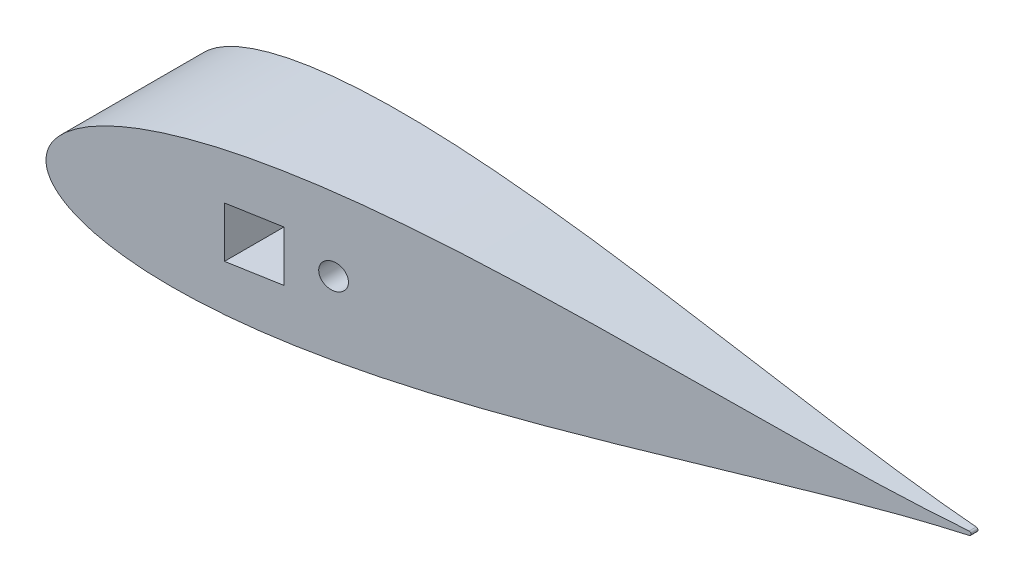
SolidWorks part; units mm, degrees
ref_plane "Front Plane" through (0, 0, 0) normal (0, 0, 1) x (1, 0, 0)
ref_plane "Top Plane" through (0, 0, 0) normal (0, 1, 0) x (1, 0, 0)
ref_plane "Right Plane" through (0, 0, 0) normal (1, 0, 0) x (0, 0, -1)
curve "Curve4"
  spline degree 3 poles (100, 0, 0) (99.8498, 0.0023, 0) (99.4759, 0.008, 0) (99.1023, 0.0238, 0) (98.8789, 0.0332, 0) knots 0 0 0 0 0.401829 1 1 1 1
curve "Curve5"
  spline degree 3 poles (99.3714, -0.0082, 0) (100.2526, 0, 0) (99.3714, 0.0082, 0) (98.8504, 0.035, 0) (97.904, 0.0811, 0) (96.8285, 0.1543, 0) (95.5159, 0.2583, 0) (94.013, 0.3972, 0) (92.313, 0.574, 0) (90.4281, 0.791, 0) (88.3655, 1.0495, 0) (86.1348, 1.3497, 0) (83.7456, 1.691, 0) (81.2082, 2.0715, 0) (78.5335, 2.4886, 0) (75.7326, 2.9386, 0) (72.8172, 3.4168, 0) (69.799, 3.9177, 0) (66.6904, 4.435, 0) (63.5039, 4.9616, 0) (60.2521, 5.4899, 0) (56.948, 6.0119, 0) (53.6049, 6.519, 0) (50.2363, 7.0024, 0) (46.8558, 7.4534, 0) (43.4774, 7.8632, 0) (40.1152, 8.2232, 0) (36.7837, 8.5249, 0) (33.4975, 8.7606, 0) (30.2716, 8.923, 0) (27.1211, 9.0055, 0) (24.0614, 9.0025, 0) (21.108, 8.909, 0) (18.277, 8.7213, 0) (15.5843, 8.4369, 0) (13.0466, 8.0543, 0) (10.6806, 7.5735, 0) (8.5039, 6.996, 0) (6.5349, 6.3253, 0) (4.7933, 5.5673, 0) (3.3001, 4.7321, 0) (2.0777, 3.8366, 0) (1.1467, 2.91, 0) (0.5165, 2.0014, 0) (0.165, 1.1816, 0) (0.0231, 0.524, 0) (-0.0093, 0, 0) (0.0231, -0.524, 0) (0.165, -1.1816, 0) (0.5165, -2.0014, 0) (1.1467, -2.91, 0) (2.0777, -3.8366, 0) (3.3001, -4.7321, 0) (4.7933, -5.5673, 0) (6.5349, -6.3253, 0) (8.5039, -6.996, 0) (10.6806, -7.5735, 0) (13.0466, -8.0543, 0) (15.5843, -8.4369, 0) (18.277, -8.7213, 0) (21.108, -8.909, 0) (24.0614, -9.0025, 0) (27.1211, -9.0055, 0) (30.2716, -8.923, 0) (33.4975, -8.7606, 0) (36.7837, -8.5249, 0) (40.1152, -8.2232, 0) (43.4774, -7.8632, 0) (46.8558, -7.4534, 0) (50.2363, -7.0024, 0) (53.6049, -6.519, 0) (56.948, -6.0119, 0) (60.2521, -5.4899, 0) (63.5039, -4.9616, 0) (66.6904, -4.435, 0) (69.799, -3.9177, 0) (72.8172, -3.4168, 0) (75.7326, -2.9386, 0) (78.5335, -2.4886, 0) (81.2082, -2.0715, 0) (83.7456, -1.691, 0) (86.1348, -1.3497, 0) (88.3655, -1.0495, 0) (90.4281, -0.791, 0) (92.313, -0.574, 0) (94.013, -0.3972, 0) (95.5159, -0.2583, 0) (96.8285, -0.1543, 0) (97.904, -0.0811, 0) (98.8504, -0.035, 0) (99.3714, -0.0082, 0) (100.2526, 0, 0) (99.3714, 0.0082, 0) knots -0.009667 -0.005395 -0.002168 0 0.002168 0.005395 0.009667 0.014967 0.021271 0.028553 0.036781 0.04592 0.055932 0.066773 0.078397 0.090755 0.103793 0.117456 0.131686 0.146422 0.1616 0.177156 0.193024 0.209135 0.225421 0.241812 0.258238 0.274629 0.290914 0.307025 0.322893 0.338448 0.353626 0.368361 0.38259 0.396253 0.40929 0.421647 0.43327 0.444109 0.454119 0.463255 0.471479 0.478755 0.485052 0.490344 0.49461 0.497833 0.5 0.502167 0.50539 0.509656 0.514948 0.521245 0.528521 0.536745 0.545881 0.555891 0.56673 0.578353 0.59071 0.603747 0.61741 0.631639 0.646374 0.661552 0.677107 0.692975 0.709086 0.725371 0.741762 0.758188 0.774579 0.790865 0.806976 0.822844 0.8384 0.853578 0.868314 0.882544 0.896207 0.909245 0.921603 0.933227 0.944068 0.95408 0.963219 0.971447 0.978729 0.985033 0.990333 0.994605 0.997832 1 1.002168 1.005395 1.009667 periodic
sketch "Sketch2" plane through (0, 0, 0) normal (0, 0, 1) x (1, 0, 0)
  line L0 (642.3793, 0) -> (0, 0) construction
  circle A14 centre (642.3793, 0) radius 1.5875 construction
  arc A15 (642.5108, -1.582) -> (642.5108, 1.582) centre (642.3793, 0) ccw
  spline S2 degree 3 poles (666.3448, -0.0547) (672.2538, 0) (666.3448, 0.0547) (662.8509, 0.2344) (656.505, 0.5436) (649.293, 1.0348) (640.4916, 1.7319) (630.4138, 2.6634) (619.0141, 3.8493) (606.375, 5.3044) (592.5439, 7.0376) (577.5855, 9.0506) (561.5643, 11.3389) (544.5497, 13.8907) (526.6141, 16.6877) (507.8326, 19.7051) (488.2827, 22.9117) (468.0444, 26.2704) (447.1994, 29.739) (425.8316, 33.2703) (404.0263, 36.8132) (381.8707, 40.3133) (359.4533, 43.7135) (336.8645, 46.9554) (314.1962, 49.9798) (291.5418, 52.7277) (268.9963, 55.1412) (246.6566, 57.1646) (224.6209, 58.7452) (202.9892, 59.8341) (181.8631, 60.3875) (161.3458, 60.367) (141.542, 59.7399) (122.5581, 58.4818) (104.5023, 56.5743) (87.485, 54.0089) (71.6197, 50.7848) (57.0237, 46.9125) (43.8205, 42.415) (32.1416, 37.3322) (22.1291, 31.7315) (13.9324, 25.7264) (7.6896, 19.5132) (3.4631, 13.4204) (1.1063, 7.9234) (0.1546, 3.5138) (-0.0622, 0) (0.1546, -3.5138) (1.1063, -7.9234) (3.4631, -13.4204) (7.6896, -19.5132) (13.9324, -25.7264) (22.1291, -31.7315) (32.1416, -37.3322) (43.8205, -42.415) (57.0237, -46.9125) (71.6197, -50.7848) (87.485, -54.0089) (104.5023, -56.5743) (122.5581, -58.4818) (141.542, -59.7399) (161.3458, -60.367) (181.8631, -60.3875) (202.9892, -59.8341) (224.6209, -58.7452) (246.6566, -57.1646) (268.9963, -55.1412) (291.5418, -52.7277) (314.1962, -49.9798) (336.8645, -46.9554) (359.4533, -43.7135) (381.8707, -40.3133) (404.0263, -36.8132) (425.8316, -33.2703) (447.1994, -29.739) (468.0444, -26.2704) (488.2827, -22.9117) (507.8326, -19.7051) (526.6141, -16.6877) (544.5497, -13.8907) (561.5643, -11.3389) (577.5855, -9.0506) (592.5439, -7.0376) (606.375, -5.3044) (619.0141, -3.8493) (630.4138, -2.6634) (640.4916, -1.7319) (649.293, -1.0348) (656.505, -0.5436) (662.8509, -0.2344) (666.3448, -0.0547) (672.2538, 0) (666.3448, 0.0547) knots -0.009667 -0.005395 -0.002168 0 0.002168 0.005395 0.009667 0.014967 0.021271 0.028553 0.036781 0.04592 0.055932 0.066773 0.078397 0.090755 0.103793 0.117456 0.131686 0.146422 0.1616 0.177156 0.193024 0.209135 0.225421 0.241812 0.258238 0.274629 0.290914 0.307025 0.322893 0.338448 0.353626 0.368361 0.38259 0.396253 0.40929 0.421647 0.43327 0.444109 0.454119 0.463255 0.471479 0.478755 0.485052 0.490344 0.49461 0.497833 0.5 0.502167 0.50539 0.509656 0.514948 0.521245 0.528521 0.536745 0.545881 0.555891 0.56673 0.578353 0.59071 0.603747 0.61741 0.631639 0.646374 0.661552 0.677107 0.692975 0.709086 0.725371 0.741762 0.758188 0.774579 0.790865 0.806976 0.822844 0.8384 0.853578 0.868314 0.882544 0.896207 0.909245 0.921603 0.933227 0.944068 0.95408 0.963219 0.971447 0.978729 0.985033 0.990333 0.994605 0.997832 1 1.002168 1.005395 1.009667 only from (670.56, 0) to (670.56, 0)
  point P8 (1.2169, -4.6585)
  point P10 (1.2169, 4.6585)
  dimension "D10" = 3.175
extrude "Boss-Extrude1" add sketch "Sketch2" along normal blind 127
extrude "Cut-Extrude4" cut sketch "Sketch7" against normal through all
sketch "Sketch7" plane through (327.9592, -13.7514, 6.35) normal (0, 0, 1) x (1, 0, 0)
  line L1 (-154.9852, -16.7286) -> (-66.0852, -16.7286)
  line L2 (-154.9852, -16.7286) -> (-154.9852, 44.2314)
  line L3 (-154.9852, 44.2314) -> (-66.0852, 44.2314)
  line L4 (-66.0852, -16.7286) -> (-66.0852, 44.2314)
  line L5 (-154.9852, -16.7286) -> (-66.0852, 44.2314) construction
  line L6 (-154.9852, 44.2314) -> (-66.0852, -16.7286) construction
  point P0 (-110.5352, 13.7514)
extrude "Cut-Extrude5" cut sketch "Sketch8" against normal through all
sketch "Sketch8" plane through (327.9592, -13.7514, 6.35) normal (0, 0, 1) x (1, 0, 0)
  circle A0 centre (314.9285, 13.7514) radius 1.2446
scale "Scale1" scale about origin uniform scaling yes scale factor 0.46
sketch "Sketch10" plane through (0, 0, 58.42) normal (0, 0, 1) x (1, 0, 0)
  line L1 (57.15, -9.525) -> (76.2, -9.525)
  line L2 (57.15, -9.525) -> (57.15, 9.525)
  line L3 (57.15, 9.525) -> (76.2, 9.525)
  line L4 (76.2, -9.525) -> (76.2, 9.525)
  line L5 (57.15, -9.525) -> (76.2, 9.525) construction
  line L6 (57.15, 9.525) -> (76.2, -9.525) construction
  circle A0 centre (92.075, 0) radius 4.7625
  point P0 (66.675, 0)
  dimension "D3" = 9.525
  dimension "D4" = 15.875
  dimension "D1" = 19.05
  dimension "D2" = 57.15
extrude "Cut-Extrude6" cut sketch "Sketch10" against normal through all
sketch "Sketch11" [suppressed] plane through (0, 0, 2.2225) normal (0, 0, 1) x (1, 0, 0)
  line L1 (22.225, 9.525) -> (41.275, 9.525)
  line L2 (22.225, 9.525) -> (22.225, -9.525)
  line L3 (22.225, -9.525) -> (41.275, -9.525)
  line L4 (41.275, 9.525) -> (41.275, -9.525)
  line L5 (22.225, 9.525) -> (41.275, -9.525) construction
  line L6 (22.225, -9.525) -> (41.275, 9.525) construction
  point P0 (31.75, 0)
  dimension "D1" = 19.05
  dimension "D2" = 22.225
extrude "Cut-Extrude7" [suppressed] cut sketch "Sketch11" against normal through all
sketch "Sketch12" [suppressed] plane through (0, 0, 0) normal (0, 0, 1) x (1, 0, 0)
  line L1 (114.3, -9.525) -> (133.35, -9.525)
  line L2 (114.3, -9.525) -> (114.3, 9.525)
  line L3 (114.3, 9.525) -> (133.35, 9.525)
  line L4 (133.35, -9.525) -> (133.35, 9.525)
  line L5 (114.3, -9.525) -> (133.35, 9.525) construction
  line L6 (114.3, 9.525) -> (133.35, -9.525) construction
  point P0 (123.825, 0)
  dimension "D1" = 19.05
  dimension "D2" = 114.3
extrude "Cut-Extrude10" [suppressed] cut sketch "Sketch12" along normal blind 2.54
sketch "Sketch13" plane through (0, 0, 0) normal (0, 1, 0) x (1, 0, 0)
  line L1 (0, 0) -> (0, -58.42) construction
  line L2 (0, -54.7724) -> (296.2247, -2.54)
  line L3 (296.2247, -2.54) -> (296.2247, 0)
  line L7 (0, -54.7724) -> (0, -58.42)
  line L8 (0, -58.42) -> (296.2247, -58.42)
  line L9 (296.2247, -58.42) -> (296.2247, -2.54)
  dimension "D1" = 10
  dimension "D2" = 2.54
extrude "Cut-Extrude11" cut sketch "Sketch13" against normal through all both and the other way through all contours L9 L8 L7 L2
equation "\"0.5n\"=0"
